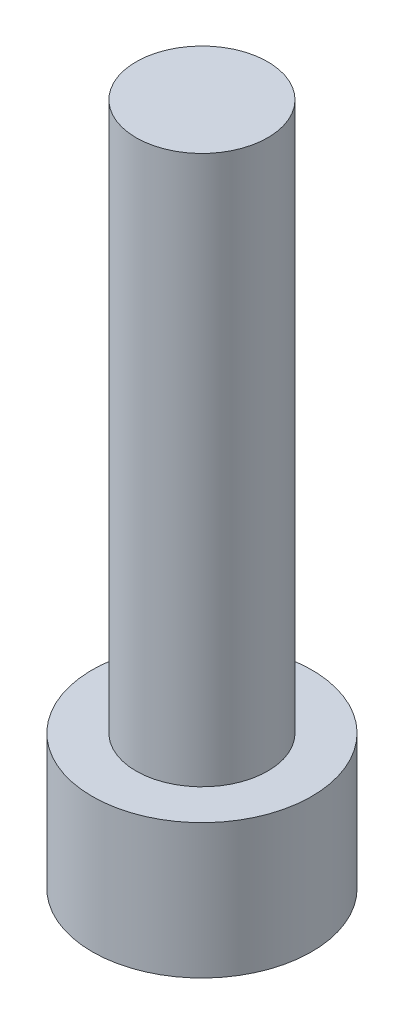
SolidWorks part; units mm, degrees
ref_plane "Front Plane" through (0, 0, 0) normal (0, 0, 1) x (1, 0, 0)
ref_plane "Top Plane" through (0, 0, 0) normal (0, 1, 0) x (1, 0, 0)
ref_plane "Right Plane" through (0, 0, 0) normal (1, 0, 0) x (0, 0, -1)
sketch "Sketch1" plane through (0, 0, 0) normal (0, 1, 0) x (1, 0, 0)
  circle A0 centre (0, 0) radius 2.8575
  dimension "D1" = 5.715
extrude "Boss-Extrude1" add sketch "Sketch1" along normal blind 3.5052
sketch "Sketch2" plane through (0, 0, 0) normal (0, -1, 0) x (1, 0, 0)
  line L1 (1.604, 0) -> (0.802, 1.3891)
  line L2 (0.802, 1.3891) -> (-0.802, 1.3891)
  line L3 (-0.802, 1.3891) -> (-1.604, 0)
  line L4 (-1.604, 0) -> (-0.802, -1.3891)
  line L5 (-0.802, -1.3891) -> (0.802, -1.3891)
  line L6 (0.802, -1.3891) -> (1.604, 0)
  circle A0 centre (0, 0) radius 1.3891 construction
  dimension "D1" = 2.7781
extrude "Cut-Extrude1" cut sketch "Sketch2" against normal blind 1.9558
sketch "Sketch3" plane through (0, 3.5052, 0) normal (0, 1, 0) x (1, 0, 0)
  circle A0 centre (0, 0) radius 1.7145
  dimension "D1" = 3.429
extrude "Boss-Extrude2" add sketch "Sketch3" along normal blind 14.2875
